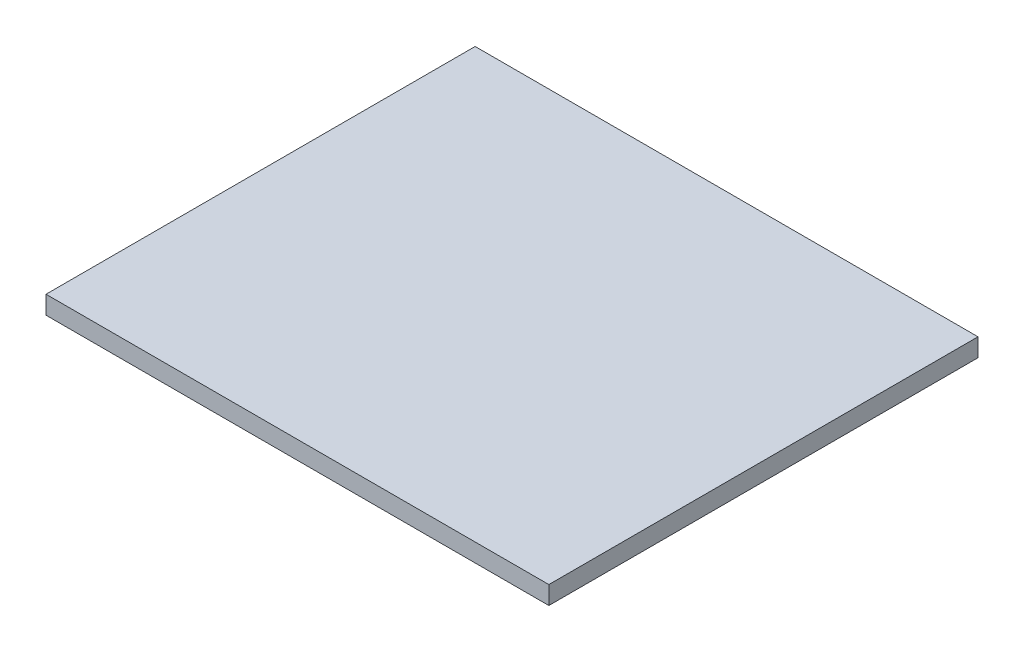
SolidWorks part; units mm, degrees
ref_plane "Спереди" through (0, 0, 0) normal (0, 0, 1) x (1, 0, 0)
ref_plane "Сверху" through (0, 0, 0) normal (0, 1, 0) x (1, 0, 0)
ref_plane "Справа" through (0, 0, 0) normal (1, 0, 0) x (0, 0, -1)
sketch "Эскиз1" plane through (0, 0, 0) normal (0, 1, 0) x (1, 0, 0)
  line L1 (249, -212.5) -> (-249, -212.5)
  line L2 (249, -212.5) -> (249, 212.5)
  line L3 (249, 212.5) -> (-249, 212.5)
  line L4 (-249, -212.5) -> (-249, 212.5)
  line L5 (249, -212.5) -> (-249, 212.5) construction
  line L6 (249, 212.5) -> (-249, -212.5) construction
  point P0 (0, 0)
  dimension "D1" = 498
  dimension "D2" = 425
extrude "Бобышка-Вытянуть1" add sketch "Эскиз1" along normal blind 18
